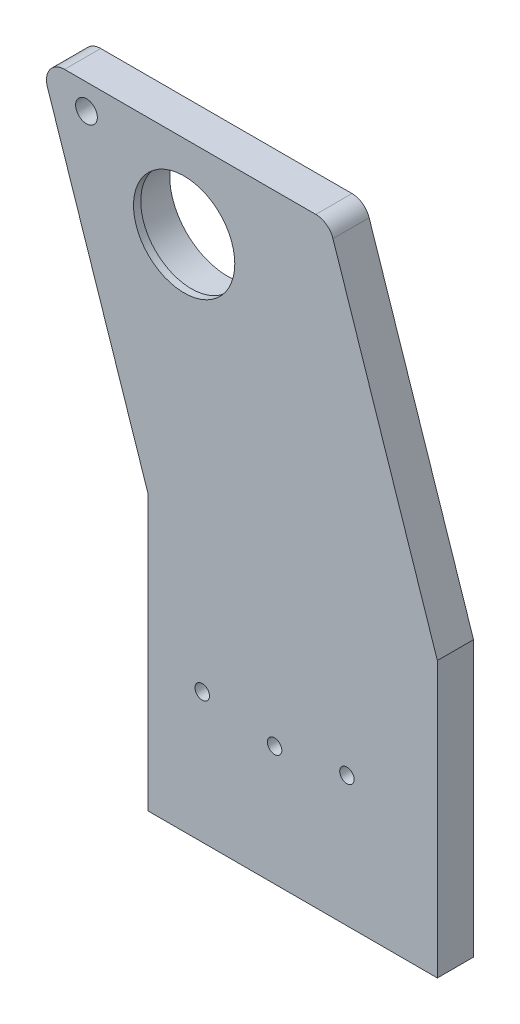
SolidWorks part; units mm, degrees
material "Alloy Steel (SS)"
ref_plane "Front Plane" through (0, 0, 0) normal (0, 0, 1) x (1, 0, 0)
ref_plane "Top Plane" through (0, 0, 0) normal (0, 1, 0) x (1, 0, 0)
ref_plane "Right Plane" through (0, 0, 0) normal (1, 0, 0) x (0, 0, -1)
sketch "Sketch1" plane through (0, 0, 0) normal (0, 0, 1) x (1, 0, 0)
  line L0 (-40, 83) -> (-70, 83)
  line L1 (10, 83) -> (-40, 83)
  line L2 (40, -7) -> (40, -83)
  line L3 (40, -83) -> (-40, -83)
  line L4 (-40, -7) -> (-40, -83)
  line L5 (40, 83) -> (-40, -83) construction
  line L6 (40, -83) -> (-40, 83) construction
  line L7 (-70, 83) -> (-40, -7)
  line L8 (40, 83) -> (40, -7) construction
  line L9 (10, 83) -> (40, -7)
  circle A0 centre (-30, 60) radius 16
  point P0 (0, 0)
  point P12 (-40, -80)
  dimension "D10" = 32
  dimension "D1" = 80
  dimension "D2" = 166
  dimension "D3" = 30
  dimension "D4" = 90
  dimension "D5" = 30
  dimension "D6" = 90
  dimension "D7" = 83
  dimension "D8" = 83
  dimension "D9" = 40
  dimension "D11" = 30
  dimension "D12" = 143
  dimension "D13" = 163
extrude "Boss-Extrude1" add sketch "Sketch1" along normal blind 10
sketch "Sketch2" plane through (0, 0, 10) normal (0, 0, 1) x (1, 0, 0)
  circle A0 centre (-30, 60) radius 16
  circle A1 centre (-30, 60) radius 18
  dimension "D1" = 36
  dimension "D2" = 32
extrude "Boss-Extrude2" add sketch "Sketch2" against normal blind 12
sketch "Sketch3" plane through (0, 0, 10) normal (0, 0, 1) x (1, 0, 0)
  line L0 (-40, -7) -> (-40, -83) construction
  line L1 (-40, -83) -> (40, -83) construction
  circle A0 centre (-25, -47) radius 2
  circle A1 centre (15, -47) radius 2
  dimension "D3" = 4
  dimension "D4" = 4
  dimension "D1" = 15
  dimension "D2" = 40
  dimension "D5" = 36
extrude "Cut-Extrude1" cut sketch "Sketch3" against normal blind 10
sketch "Sketch4" plane through (0, 0, 10) normal (0, 0, 1) x (1, 0, 0)
  line L0 (10, 83) -> (-70, 83) construction
  circle A0 centre (-57, 76) radius 3
  dimension "D1" = 6
  dimension "D2" = 13
  dimension "D3" = 7
extrude "Cut-Extrude2" cut sketch "Sketch4" against normal up to next
sketch "Sketch5" plane through (0, 0, 0) normal (0, 0, -1) x (-1, 0, 0)
  line L0 (40, -83) -> (-40, -83) construction
  line L1 (-40, -83) -> (-40, -7) construction
  circle A0 centre (5, -50) radius 2
  dimension "D3" = 4
  dimension "D1" = 33
  dimension "D2" = 45
extrude "Cut-Extrude3" cut sketch "Sketch5" against normal up to next
fillet "Fillet1" radius 5 2 edges at (10, 83, 5) (-70, 83, 5)
sketch "Sketch6" plane through (0, 0, 10) normal (0, 0, 1) x (1, 0, 0)
  point P0 (-30, 60)
sketch "Sketch7" plane through (0, 0, 10) normal (0, 0, 1) x (1, 0, 0)
  circle A1 centre (-30, 60) radius 16 construction
  circle A2 centre (-30, 60) radius 14
  circle A3 centre (-30, 60) radius 14
  circle A4 centre (-30, 60) radius 16
  dimension "D1" = 2
extrude "Boss-Extrude3" add sketch "Sketch7" along normal blind 2 from offset 2
